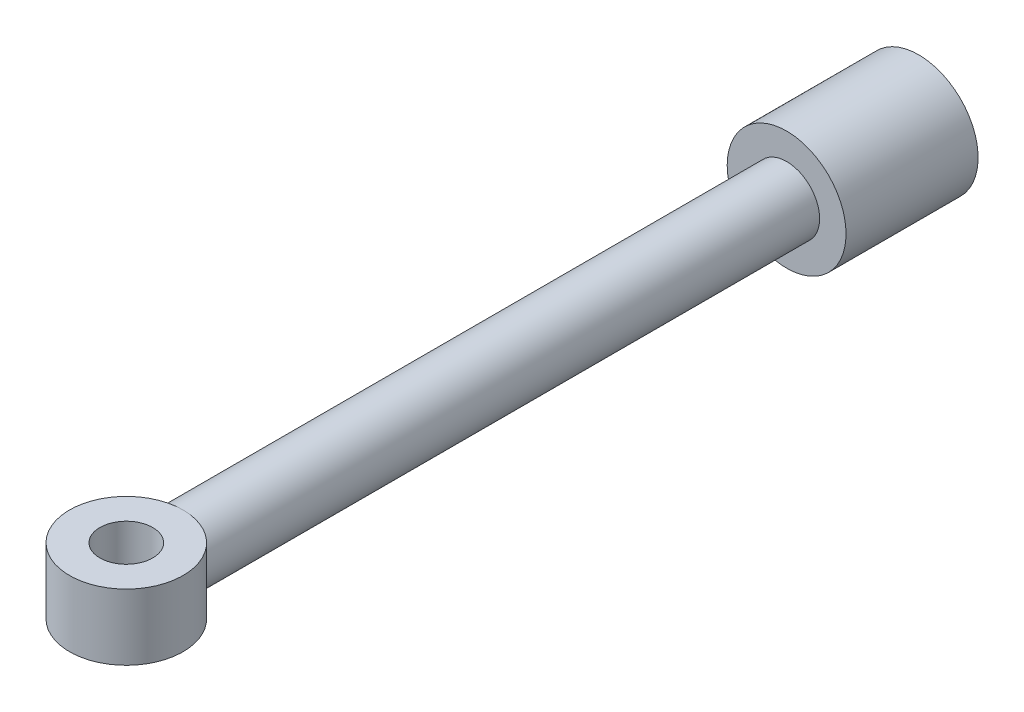
SolidWorks part; units mm, degrees
material "AISI 4340 Steel, normalized"
ref_plane "Front Plane" through (0, 0, 0) normal (0, 0, 1) x (1, 0, 0)
ref_plane "Top Plane" through (0, 0, 0) normal (0, 1, 0) x (1, 0, 0)
ref_plane "Right Plane" through (0, 0, 0) normal (1, 0, 0) x (0, 0, -1)
sketch "Sketch1" plane through (0, 0, 0) normal (0, 1, 0) x (1, 0, 0)
  line L0 (0, -75) -> (0, -675) construction
  line L1 (0, -75) -> (45, -75)
  line L4 (45, -75) -> (45, -175)
  line L5 (45, -175) -> (25, -175)
  line L6 (25, -175) -> (25, -640.0143)
  line L7 (25, -640.0143) -> (0, -640.0143)
  line L8 (0, -640.0143) -> (0, -75)
  circle A0 centre (0, -675) radius 20 construction
  circle A1 centre (0, -675) radius 43 construction
  circle A2 centre (0, 0) radius 20 construction
  dimension "D1" = 86
  dimension "D2" = 600
  dimension "D3" = 50
  dimension "D4" = 100
  dimension "D5" = 45
  dimension "D7" = 75
revolve "Revolve1" add sketch "Sketch1" angle 360 about L0
sketch "Sketch3" plane through (0, 0, 0) normal (0, 1, 0) x (1, 0, 0)
  circle A0 centre (0, -675) radius 20
  circle A1 centre (0, -675) radius 43
  circle A2 centre (0, -675) radius 43 construction
  circle A3 centre (0, -675) radius 20 construction
extrude "Boss-Extrude1" add sketch "Sketch3" along normal mid plane 50
